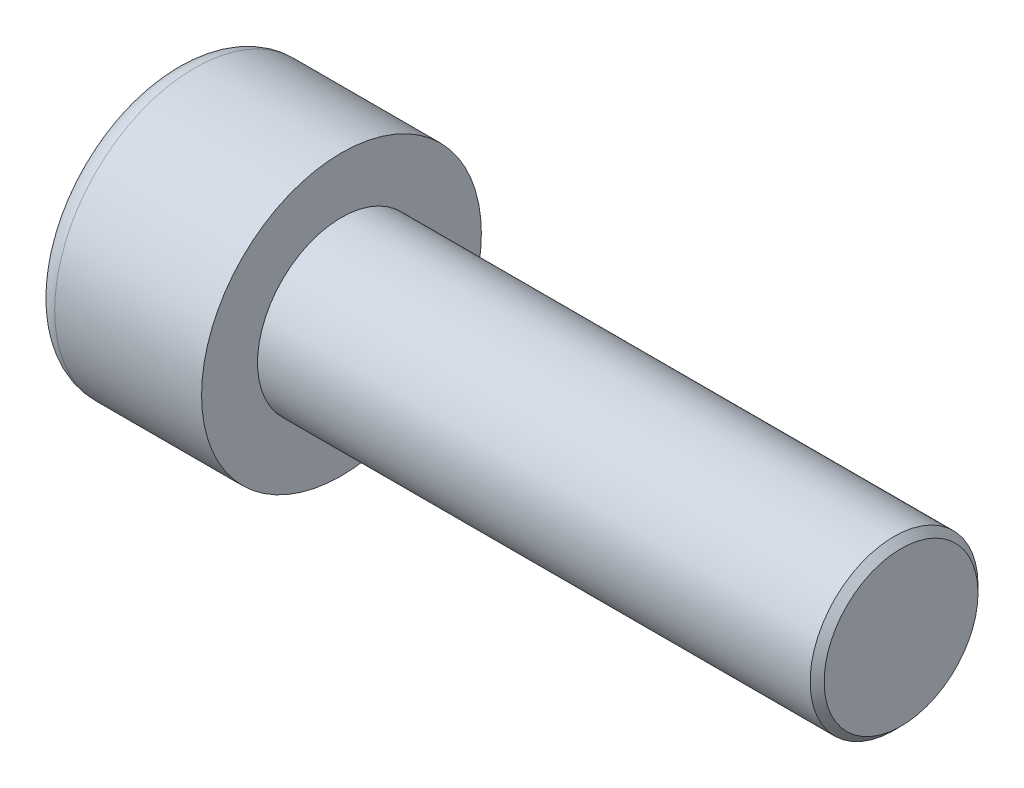
SolidWorks part; units mm, degrees
ref_plane "Front" through (0, 0, 0) normal (0, 0, 1) x (1, 0, 0)
ref_plane "Top" through (0, 0, 0) normal (0, 1, 0) x (1, 0, 0)
ref_plane "Right" through (0, 0, 0) normal (1, 0, 0) x (0, 0, -1)
sketch "Sketch1" plane through (0, 0, 0) normal (1, 0, 0) x (0, 0, -1)
  circle A0 centre (0, 0) radius 5
  dimension "dk" = 10
extrude "BaseHead" add sketch "Sketch1" along normal blind 6
sketch "Sketch2" plane through (6, 0, 0) normal (1, 0, 0) x (0, 0, -1)
  circle A0 centre (0, 0) radius 3
  dimension "d" = 6
extrude "BaseBody" add sketch "Sketch2" along normal blind 20
cosmetic thread "ThreadCosmetic1" [suppressed] parameters "b"=24, "D2"=4.917
sketch "Sketch3" plane through (0, 0, 0) normal (1, 0, 0) x (0, 0, -1)
  line L1 (2.8868, 0) -> (1.4434, 2.5)
  line L2 (1.4434, 2.5) -> (-1.4434, 2.5)
  line L3 (-1.4434, 2.5) -> (-2.8868, 0)
  line L4 (-2.8868, 0) -> (-1.4434, -2.5)
  line L5 (-1.4434, -2.5) -> (1.4434, -2.5)
  line L6 (1.4434, -2.5) -> (2.8868, 0)
  circle A0 centre (0, 0) radius 2.5 construction
  dimension "s" = 5
  dimension "e" = 5.7735
extrude "HexagonSocket" cut sketch "Sketch3" along normal blind 3
sketch "Sketch4" plane through (-4.1961, 0.75, 0) normal (0, 0, 1) x (-1, 0, 0)
  line L0 (-7.1961, 3.25) -> (-8.6395, 0.75)
  line L2 (-8.6395, 0.75) -> (-7.1961, 0.75)
  line L3 (-7.1961, 0.75) -> (-7.1961, 3.25)
  line L4 (-5.0351, 0.75) -> (0.839, 0.75) construction
  line L5 (-30.1961, 0.75) -> (-10.1961, 0.75) construction
  line L6 (-10.1961, 0.75) -> (-4.1961, 0.75) construction
  dimension "m" = 60
revolve "Cut-Revolve1" cut sketch "Sketch4" angle 360 about L4
fillet "HeadFillet" [suppressed] radius 0.25
fillet "TopFillet" radius 0.75 1 edges at (0, 0, -5)
chamfer "Chamfer1" distance 0.25 angle 45 1 edges at (26, 0, -3)
sketch "Sketch5" plane through (0, 0, 0) normal (0, 0, 1) x (1, 0, 0)
  line L0 (25.75, 2.531) -> (26.0207, 3)
  line L1 (26.0207, 3) -> (26.0207, 3.5415)
  line L2 (26.0207, 3.5415) -> (25.4792, 3.5415)
  line L3 (25.4792, 3.5415) -> (25.4792, 3)
  line L4 (25.4792, 3) -> (25.75, 2.531)
  line L5 (0, 0) -> (7.8886, 0) construction
  line L6 (25.75, -3) -> (25.75, 3) construction
  dimension "D1" = 6
  dimension "D2" = 0.5415
revolve "Cut-Revolve10" [suppressed] cut sketch "Sketch5" angle 360 about L5
pattern_linear "LPattern10" [suppressed] count 37 spacing 0.6498 along (1, 0, 0)
equation "\"r1@TopFillet\" = \"d@Sketch2\" / 8"
equation "\"D1@Chamfer1\" = \"r@HeadFillet\""
equation "\"D1@Sketch5\" = \"d@Sketch2\""
equation "\"D2@Sketch5\" =  ( \"d@Sketch2\" - \"D2@ThreadCosmetic1\" )  / 2"
equation "\"D3@LPattern10\" = \"D2@Sketch5\" * 1.2"
equation "\"D1@LPattern10\" = \"b@ThreadCosmetic1\" / \"D3@LPattern10\""
